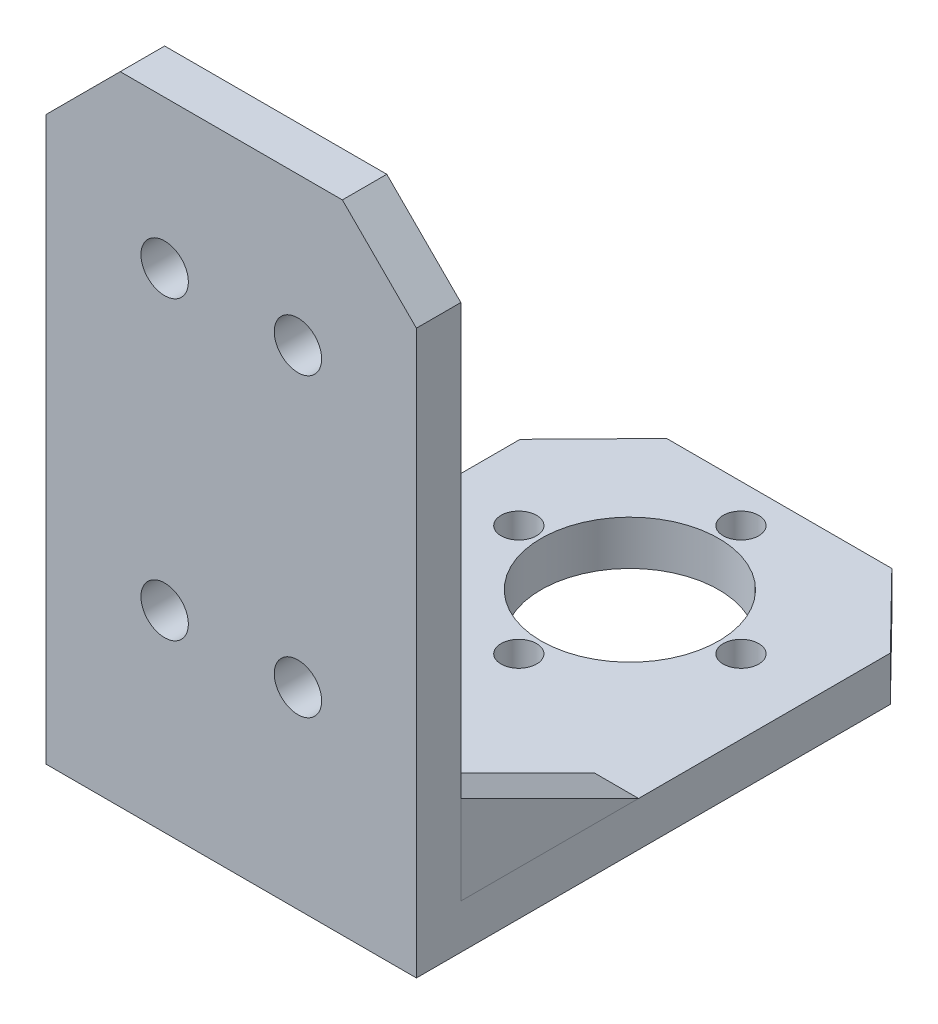
SolidWorks part; units mm, degrees
material "PLA"
ref_plane "Front Plane" through (0, 0, 0) normal (0, 0, 1) x (1, 0, 0)
ref_plane "Top Plane" through (0, 0, 0) normal (0, 1, 0) x (1, 0, 0)
ref_plane "Right Plane" through (0, 0, 0) normal (1, 0, 0) x (0, 0, -1)
sketch "Sketch2" plane through (0, 0, 0) normal (0, 1, 0) x (1, 0, 0)
  line L3 (-25.2811, -53.722) -> (-50.2811, -53.722)
  line L5 (-50.2811, -21.722) -> (-50.2811, -53.722)
  line L6 (-50.2811, -21.722) -> (-45.3821, -16.722)
  line L7 (-30.1801, -16.722) -> (-45.3821, -16.722)
  line L8 (-25.2811, -21.722) -> (-25.2811, -53.722)
  line L9 (-30.1801, -16.722) -> (-25.2811, -21.722)
  circle A2 centre (-37.7811, -26.8075) radius 6
  circle A3 centre (-37.7811, -26.8075) radius 7.5 construction
  circle A4 centre (-37.7811, -19.3075) radius 1.2
  circle A5 centre (-45.2811, -26.8075) radius 1.2
  circle A6 centre (-37.7811, -34.3075) radius 1.2
  circle A7 centre (-30.2811, -26.8075) radius 1.2
  point P0 (-37.7811, -16.722)
  dimension "D3" = 10.0855
  dimension "D4" = 32
  dimension "D1" = 25
  dimension "D2" = 5
extrude "Boss-Extrude1" add sketch "Sketch2" along normal blind 3
sketch "Sketch4" plane through (0, 3, 0) normal (0, 1, 0) x (1, 0, 0)
  line L0 (-25.2811, -53.722) -> (-25.2811, -21.722) construction
  line L1 (-50.2811, -53.722) -> (-25.2811, -53.722)
  line L2 (-50.2811, -53.722) -> (-50.2811, -50.722)
  line L3 (-50.2811, -50.722) -> (-25.2811, -50.722)
  line L4 (-25.2811, -53.722) -> (-25.2811, -50.722)
extrude "Boss-Extrude2" add sketch "Sketch4" along normal blind 40
sketch "Sketch5" plane through (0, 0, 50.722) normal (0, 0, -1) x (-1, 0, 0)
  line L0 (25.2811, 43) -> (25.2811, 38)
  line L1 (25.2811, 43) -> (25.2811, 3) construction
  line L2 (25.2811, 38) -> (30.2811, 43)
  line L3 (25.2811, 43) -> (50.2811, 43) construction
  line L4 (30.2811, 43) -> (25.2811, 43)
  line L5 (50.2811, 43) -> (45.2811, 43)
  line L6 (45.2811, 43) -> (50.2811, 38)
  line L7 (50.2811, 43) -> (50.2811, 3) construction
  line L8 (50.2811, 38) -> (50.2811, 43)
  dimension "D1" = 5
  dimension "D2" = 5
  dimension "D3" = 5
  dimension "D4" = 5
extrude "Cut-Extrude1" cut sketch "Sketch5" against normal blind 8
hole_wizard "Ø3.2 (3.2) Diameter Hole1" positions "Sketch8" profile "Sketch9" hole size "Ø3.2" standard "ANSI Metric"
sketch "Sketch8" plane through (0, 0, 50.722) normal (0, 0, -1) x (-1, 0, 0)
  line L0 (30.2811, 43) -> (45.2811, 43) construction
  line L1 (25.2811, 3) -> (50.2811, 3) construction
  line L2 (50.2811, 38) -> (50.2811, 3) construction
  line L3 (50.2811, 38) -> (50.2811, 0) construction
  line L4 (25.2811, 38) -> (25.2811, 3) construction
  point P0 (33.2811, 33)
  point P2 (42.2811, 33)
  point P4 (42.2811, 13)
  point P6 (33.2811, 13)
  dimension "D1" = 10
  dimension "D2" = 10
  dimension "D3" = 10
  dimension "D4" = 10
  dimension "D5" = 8
  dimension "D6" = 8
  dimension "D7" = 8
  dimension "D8" = 8
sketch "Sketch9" plane through (-33.2811, 33, 50.722) normal (1, 0, 0) x (0, 1, 0)
  line L0 (0, 0) -> (0, 4.1614)
  line L1 (0, 4.1614) -> (1.6, 3.2)
  line L2 (1.6, 3.2) -> (1.6, 0)
  line L5 (1.6, 0) -> (0, 0)
  line L10 (0, 4.1614) -> (-1.6, 3.2) construction
  line L11 (0, -6.35) -> (0, 107.95) construction
  dimension "Hole Dia." = 3.2
  dimension "Hole Depth" = 3.2
  dimension "Drill Angle" = 118
other "Gusset1" parameters "D1"=3, "D2"=3, "D3"=0, "D4"=0, "D10"=5, "D11"=12, "D12"=6, "D13"=15, "D14"=45, "D15"=15, "D16"=5, "D17"=5, "D18"=45
sketch "Sketch10" plane through (-50.2811, 3, 50.722) normal (1, 0, 0) x (0, 0, -1)
  line L0 (0, 0) -> (12, 0)
  line L1 (0, 0) -> (0, 6)
  line L2 (12, 0) -> (0, 6)
other "Gusset2" parameters "D1"=3, "D2"=3, "D3"=0, "D4"=0, "D10"=5, "D11"=6, "D12"=12, "D13"=15, "D14"=45, "D15"=15, "D16"=5, "D17"=5, "D18"=45
sketch "Sketch11" plane through (-25.2811, 3, 50.722) normal (-1, 0, 0) x (0, 0, 1)
  line L0 (0, 0) -> (0, 6)
  line L1 (0, 0) -> (-12, 0)
  line L2 (0, 6) -> (-12, 0)
